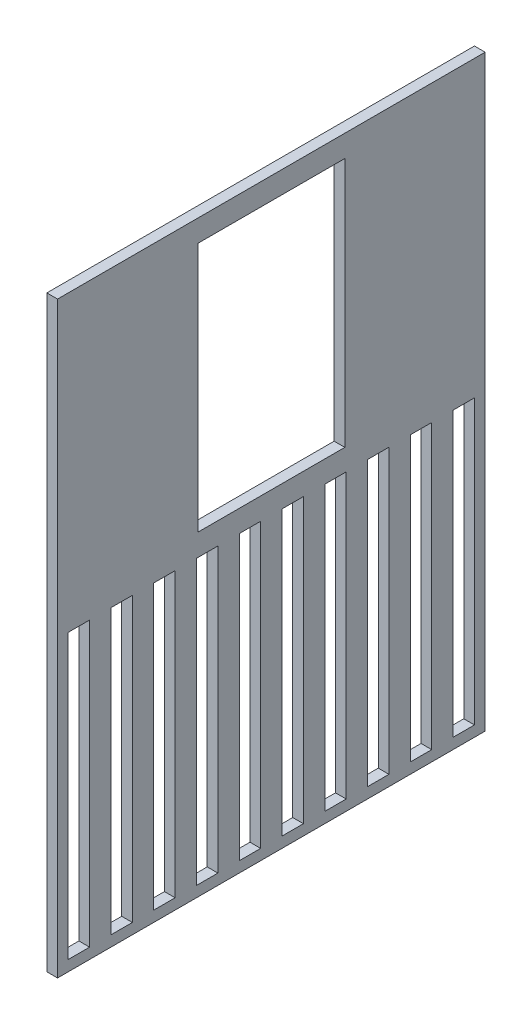
SolidWorks part; units mm, degrees
ref_plane "Front Plane" through (0, 0, 0) normal (0, 0, 1) x (1, 0, 0)
ref_plane "Top Plane" through (0, 0, 0) normal (0, 1, 0) x (1, 0, 0)
ref_plane "Right Plane" through (0, 0, 0) normal (1, 0, 0) x (0, 0, -1)
sketch "Sketch1" plane through (0, 0, 0) normal (0, 0, 1) x (1, 0, 0)
  line L1 (0, 0) -> (155, 0)
  line L2 (0, 0) -> (0, 110)
  line L3 (0, 110) -> (155, 110)
  line L4 (155, 0) -> (155, 110)
  dimension "D1" = 155
  dimension "D2" = 110
extrude "Boss-Extrude1" add sketch "Sketch1" along normal blind 80 contours L2 L1 L4 L3
sketch "Sketch2" plane through (0, 0, 80) normal (0, 0, 1) x (1, 0, 0)
  line L0 (0, 110) -> (2, 110) construction
  line L1 (0, 110) -> (155, 110) construction
  line L2 (0, 110) -> (0, 108) construction
  line L3 (0, 0) -> (0, 110) construction
  line L4 (155, 0) -> (155, 2) construction
  line L5 (155, 0) -> (155, 110) construction
  line L6 (155, 0) -> (153, 0) construction
  line L7 (0, 0) -> (155, 0) construction
  line L8 (0, 108) -> (2, 108) construction
  line L9 (2, 108) -> (2, 110) construction
  line L10 (155, 2) -> (153, 2) construction
  line L11 (153, 2) -> (153, 0) construction
  line L13 (153, 2) -> (2, 2)
  line L14 (153, 2) -> (153, 108)
  line L15 (153, 108) -> (2, 108)
  line L16 (2, 2) -> (2, 108)
  dimension "D1" = 2
  dimension "D2" = 2
  dimension "D3" = 2
  dimension "D4" = 2
extrude "Cut-Extrude1" cut sketch "Sketch2" against normal blind 78 contours L14 L13 L16 L15
sketch "Sketch3" plane through (0, 0, 2) normal (0, 0, 1) x (1, 0, 0)
  line L0 (2, 2) -> (6, 2) construction
  line L1 (153, 2) -> (2, 2) construction
  line L2 (153, 2) -> (149, 2) construction
  line L3 (2, 108) -> (6, 108) construction
  line L4 (153, 108) -> (2, 108) construction
  line L5 (2, 108) -> (2, 104.5) construction
  line L6 (2, 2) -> (2, 108) construction
  line L7 (149, 2) -> (149, 5.5) construction
  line L8 (2, 104.5) -> (6, 104.5) construction
  line L9 (6, 104.5) -> (6, 108) construction
  line L10 (6, 5.5) -> (10, 5.5) construction
  line L11 (6, 104.5) -> (149, 104.5)
  line L12 (6, 104.5) -> (6, 5.5)
  line L13 (6, 5.5) -> (149, 5.5)
  line L14 (149, 104.5) -> (149, 5.5)
  line L15 (10, 5.5) -> (10, 9.5) construction
  line L16 (149, 104.5) -> (145, 104.5) construction
  line L17 (145, 104.5) -> (145, 100.5) construction
  line L19 (10, 9.5) -> (145, 9.5)
  line L20 (10, 9.5) -> (10, 100.5)
  line L21 (10, 100.5) -> (145, 100.5)
  line L22 (145, 9.5) -> (145, 100.5)
  circle A0 centre (145, 100.5) radius 2.5
  circle A1 centre (145, 9.5) radius 2.5
  circle A2 centre (10, 9.5) radius 2.5
  circle A3 centre (10, 100.5) radius 2.5
  dimension "D10" = 5
  dimension "D11" = 5
  dimension "D12" = 5
  dimension "D13" = 5
  dimension "D1" = 4
  dimension "D2" = 3.5
  dimension "D3" = 4
  dimension "D4" = 4
  dimension "D5" = 3.5
  dimension "D6" = 4
  dimension "D7" = 4
  dimension "D8" = 4
  dimension "D9" = 4
extrude "Cut-Extrude2" cut sketch "Sketch3" against normal blind 2 contours A3 | A0 | A2 | A1
sketch "Sketch4" plane through (155, 0, 0) normal (1, 0, 0) x (0, 0, -1)
  line L1 (-53.75, 59.1) -> (-26.25, 59.1)
  line L3 (0, 55) -> (-80, 55) construction
  line L4 (0, 0) -> (0, 110) construction
  line L5 (-80, 0) -> (-80, 110) construction
  line L7 (-26.25, 105.9) -> (-26.25, 59.1)
  line L14 (-53.75, 105.9) -> (-26.25, 105.9)
  line L15 (-53.75, 105.9) -> (-53.75, 59.1)
  dimension "D1" = 46.8
  dimension "D2" = 27.5
sketch "Sketch7" plane through (0, 110, 0) normal (0, 1, 0) x (1, 0, 0)
  line L0 (0, -40) -> (155, -40) construction
  line L1 (0, -80) -> (0, 0) construction
  line L2 (155, -80) -> (155, 0) construction
  line L3 (77.5, 0) -> (77.5, -80) construction
  line L4 (0, 0) -> (155, 0) construction
  line L5 (0, -80) -> (155, -80) construction
  line L6 (110.52, -65.4) -> (95.28, -65.4) construction
  line L7 (44.48, -65.4) -> (110.52, -65.4)
  line L8 (44.48, -65.4) -> (44.48, -14.6)
  line L9 (44.48, -14.6) -> (110.52, -14.6)
  line L10 (110.52, -65.4) -> (110.52, -14.6)
  line L11 (44.48, -65.4) -> (110.52, -14.6) construction
  line L12 (44.48, -14.6) -> (110.52, -65.4) construction
  line L13 (95.28, -65.4) -> (95.28, -62.86) construction
  line L14 (110.52, -14.6) -> (95.28, -14.6) construction
  line L15 (44.48, -14.6) -> (44.48, -20.1445) construction
  line L16 (44.48, -65.4) -> (44.48, -47.62) construction
  line L17 (95.28, -14.6) -> (95.28, -17.14) construction
  line L18 (44.48, -65.4) -> (44.48, -19.68) construction
  circle A0 centre (44.48, -20.1445) radius 1.6
  circle A1 centre (95.28, -17.14) radius 1.6
  circle A2 centre (95.28, -62.86) radius 1.6
  circle A3 centre (44.48, -47.62) radius 1.6
  point P12 (77.5, -40)
  dimension "D9" = 3.2
  dimension "D10" = 3.2
  dimension "D11" = 3.2
  dimension "D12" = 3.2
  dimension "D1" = 66.04
  dimension "D2" = 50.8
  dimension "D3" = 15.24
  dimension "D4" = 2.54
  dimension "D5" = 15.24
  dimension "D6" = 2.54
  dimension "D7" = 17.78
  dimension "D8" = 45.72
extrude "Cut-Extrude7" cut sketch "Sketch7" against normal blind 2 contours A0 | A1 | A3 | A2
extrude "Cut-Extrude8" cut sketch "Sketch4" against normal blind 2
sketch "Sketch8" plane through (155, 0, 0) normal (1, 0, 0) x (0, 0, -1)
  line L0 (-80, 55) -> (0, 55) construction
  line L1 (-80, 0) -> (-80, 110) construction
  line L2 (0, 0) -> (0, 110) construction
  line L3 (0, 0) -> (-2, 0) construction
  line L4 (-80, 0) -> (0, 0) construction
  line L5 (-2, 0) -> (-2, 2) construction
  line L6 (-80, 0) -> (-78, 0) construction
  line L7 (-78, 0) -> (-78, 2) construction
  line L8 (-70, 2) -> (-70, 55)
  line L9 (-78, 2) -> (-74, 2)
  line L10 (-78, 2) -> (-78, 55)
  line L11 (-78, 55) -> (-74, 55)
  line L12 (-74, 2) -> (-74, 55)
  line L13 (-70, 2) -> (-66, 2)
  line L14 (-66, 2) -> (-66, 55)
  line L15 (-70, 55) -> (-66, 55)
  line L16 (-62, 2) -> (-62, 55)
  line L17 (-62, 2) -> (-58, 2)
  line L18 (-58, 2) -> (-58, 55)
  line L19 (-62, 55) -> (-58, 55)
  line L20 (-54, 2) -> (-54, 55)
  line L21 (-54, 2) -> (-50, 2)
  line L22 (-50, 2) -> (-50, 55)
  line L23 (-54, 55) -> (-50, 55)
  line L24 (-46, 2) -> (-46, 55)
  line L25 (-46, 2) -> (-42, 2)
  line L26 (-42, 2) -> (-42, 55)
  line L27 (-46, 55) -> (-42, 55)
  line L28 (-38, 2) -> (-38, 55)
  line L29 (-38, 2) -> (-34, 2)
  line L30 (-34, 2) -> (-34, 55)
  line L31 (-38, 55) -> (-34, 55)
  line L32 (-30, 2) -> (-30, 55)
  line L33 (-30, 2) -> (-26, 2)
  line L34 (-26, 2) -> (-26, 55)
  line L35 (-30, 55) -> (-26, 55)
  line L36 (-22, 2) -> (-22, 55)
  line L37 (-22, 2) -> (-18, 2)
  line L38 (-18, 2) -> (-18, 55)
  line L39 (-22, 55) -> (-18, 55)
  line L40 (-14, 2) -> (-14, 55)
  line L41 (-14, 2) -> (-10, 2)
  line L42 (-10, 2) -> (-10, 55)
  line L43 (-14, 55) -> (-10, 55)
  line L44 (-6, 2) -> (-6, 55)
  line L45 (-6, 2) -> (-2, 2)
  line L46 (-2, 2) -> (-2, 55)
  line L47 (-6, 55) -> (-2, 55)
  dimension "D1" = 2
  dimension "D2" = 2
  dimension "D3" = 2
  dimension "D4" = 2
  dimension "D5" = 4
extrude "Cut-Extrude9" cut sketch "Sketch8" against normal blind 2
sketch "Sketch9" plane through (0, 110, 0) normal (0, 1, 0) x (1, 0, 0)
  line L0 (0, -40) -> (155, -40) construction
  line L1 (0, -80) -> (0, 0) construction
  line L2 (155, -80) -> (155, 0) construction
  line L3 (155, -40) -> (120, -40) construction
  line L4 (120, -40) -> (120, -26) construction
  line L5 (120, -26) -> (113, -26) construction
  line L7 (113, -26) -> (127, -26)
  line L8 (113, -26) -> (113, -12)
  line L9 (113, -12) -> (127, -12)
  line L10 (127, -26) -> (127, -12)
  dimension "D1" = 35
  dimension "D2" = 14
  dimension "D3" = 7
  dimension "D4" = 14
  dimension "D5" = 14
extrude "Cut-Extrude10" cut sketch "Sketch9" against normal blind 2
sketch "Sketch10" plane through (0, 0, 0) normal (-1, 0, 0) x (0, 0, 1)
  line L0 (40, 110) -> (40, 0) construction
  line L1 (80, 110) -> (0, 110) construction
  line L2 (80, 0) -> (0, 0) construction
  line L3 (80, 55) -> (0, 55) construction
  line L4 (80, 0) -> (80, 110) construction
  line L5 (0, 0) -> (0, 110) construction
  line L6 (40, 55) -> (80, 55) construction
  line L7 (80, 55) -> (60, 55) construction
  line L8 (60, 55) -> (58, 55) construction
  line L9 (40, 95) -> (42.5, 95) construction
  line L10 (40, 15) -> (76, 15)
  line L11 (40, 15) -> (40, 95)
  line L12 (40, 95) -> (76, 95)
  line L13 (76, 15) -> (76, 95)
  line L14 (40, 15) -> (76, 95) construction
  line L15 (40, 95) -> (76, 15) construction
  line L16 (42.5, 95) -> (42.5, 92.5) construction
  line L17 (76, 15) -> (73.5, 15) construction
  line L18 (73.5, 15) -> (73.5, 17.5) construction
  line L19 (76, 15) -> (76, 19.4) construction
  line L20 (42.5, 92.5) -> (73.5, 92.5)
  line L21 (42.5, 92.5) -> (42.5, 17.5)
  line L22 (42.5, 17.5) -> (73.5, 17.5)
  line L23 (73.5, 92.5) -> (73.5, 17.5)
  line L24 (76, 19.4) -> (70.6, 19.4) construction
  line L25 (40, 95) -> (45.4, 95) construction
  line L26 (45.4, 95) -> (45.4, 90.6) construction
  line L28 (45.4, 90.6) -> (70.6, 90.6)
  line L29 (45.4, 90.6) -> (45.4, 19.4)
  line L30 (45.4, 19.4) -> (70.6, 19.4)
  line L31 (70.6, 90.6) -> (70.6, 19.4)
  circle A0 centre (73.5, 92.5) radius 1.25
  circle A1 centre (73.5, 17.5) radius 1.25
  circle A2 centre (42.5, 17.5) radius 1.25
  circle A3 centre (42.5, 92.5) radius 1.25
  dimension "D8" = 2.5
  dimension "D9" = 2.5
  dimension "D10" = 2.5
  dimension "D11" = 2.5
  dimension "D1" = 2
  dimension "D2" = 80
  dimension "D3" = 36
  dimension "D4" = 2.5
  dimension "D5" = 2.5
  dimension "D6" = 2.5
  dimension "D7" = 2.5
  dimension "D12" = 4.4
  dimension "D13" = 5.4
  dimension "D14" = 4.4
  dimension "D15" = 5.4
extrude "Cut-Extrude12" cut sketch "Sketch10" against normal blind 2 contours L31 L28 L29 L30 | A3 | A0 | A2 | A1
sketch "Sketch11" plane through (0, 0, 0) normal (-1, 0, 0) x (0, 0, 1)
  line L0 (40, 110) -> (40, 0) construction
  line L1 (80, 110) -> (0, 110) construction
  line L2 (80, 0) -> (0, 0) construction
  line L3 (20, 110) -> (20, 0) construction
  line L4 (0, 55) -> (0, 110) construction
  line L5 (0, 0) -> (0, 110) construction
  line L6 (40, 55) -> (0, 55) construction
  line L7 (0, 82.5) -> (40, 82.5) construction
  circle A0 centre (20, 55) radius 2.5
  circle A1 centre (20, 40) radius 2.5
  circle A2 centre (20, 25) radius 2.5
  circle A3 centre (20, 82.5) radius 4.5
  dimension "D1" = 5
  dimension "D3" = 9
  dimension "D2" = 3
extrude "Cut-Extrude13" cut sketch "Sketch11" against normal blind 2
sketch "Sketch12" plane through (0, 0, 80) normal (0, 0, 1) x (1, 0, 0)
  line L0 (153, 108) -> (153, 110) construction
  line L1 (0, 110) -> (155, 110) construction
  line L2 (153, 110) -> (153, 0) construction
  line L3 (0, 0) -> (155, 0) construction
  line L5 (153, 110) -> (0, 110)
  line L6 (153, 110) -> (153, 0)
  line L7 (153, 0) -> (0, 0)
  line L8 (0, 110) -> (0, 0)
extrude "Cut-Extrude14" cut sketch "Sketch12" against normal blind 80
